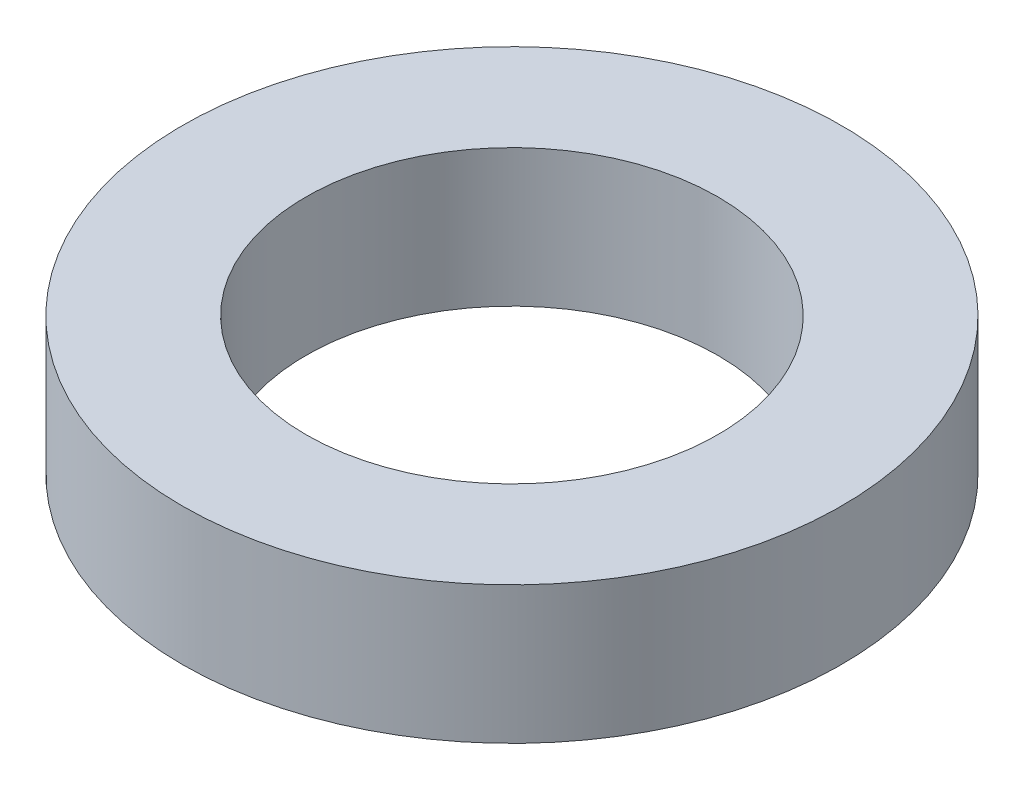
SolidWorks part; units mm, degrees
ref_plane "Front Plane" through (0, 0, 0) normal (0, 0, 1) x (1, 0, 0)
ref_plane "Top Plane" through (0, 0, 0) normal (0, 1, 0) x (1, 0, 0)
ref_plane "Right Plane" through (0, 0, 0) normal (1, 0, 0) x (0, 0, -1)
sketch "Sketch1" plane through (0, 0, 0) normal (0, 1, 0) x (1, 0, 0)
  circle A0 centre (0, 0) radius 7.5
  circle A1 centre (0, 0) radius 12
  dimension "D1" = 15
  dimension "D2" = 24
extrude "Boss-Extrude1" add sketch "Sketch1" along normal blind 5
